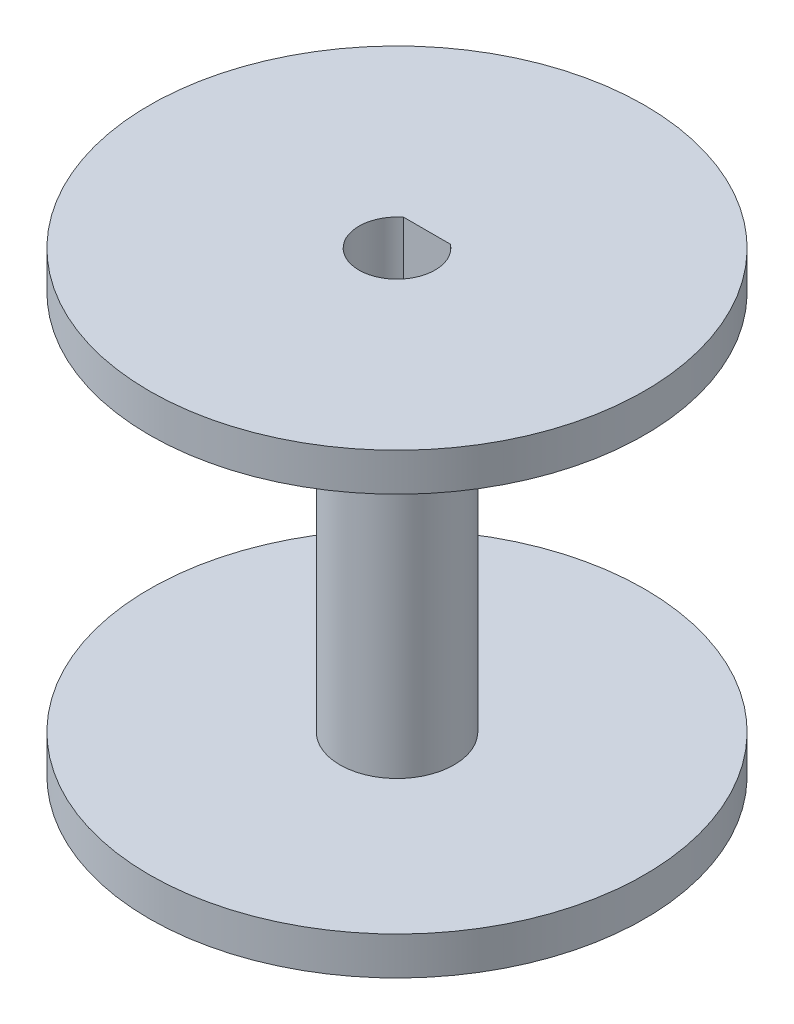
SolidWorks part; units mm, degrees
ref_plane "Front Plane" through (0, 0, 0) normal (0, 0, 1) x (1, 0, 0)
ref_plane "Top Plane" through (0, 0, 0) normal (0, 1, 0) x (1, 0, 0)
ref_plane "Right Plane" through (0, 0, 0) normal (1, 0, 0) x (0, 0, -1)
sketch "Sketch1" plane through (0, 0, 0) normal (0, 1, 0) x (1, 0, 0)
  circle A0 centre (0, 0) radius 33.02
extrude "Boss-Extrude1" add sketch "Sketch1" along normal blind 2.54
sketch "Sketch2" plane through (0, 2.54, 0) normal (0, 1, 0) x (1, 0, 0)
  circle A0 centre (0, 0) radius 2.54
  circle A1 centre (0, 0) radius 3.81
extrude "Boss-Extrude2" add sketch "Sketch2" along normal blind 25.4
sketch "Sketch3" plane through (0, 2.54, 0) normal (0, 1, 0) x (1, 0, 0)
  circle A0 centre (0, 0) radius 2.54
extrude "Cut-Extrude1" cut sketch "Sketch3" against normal blind 25.4
sketch "Sketch4" plane through (0, 27.94, 0) normal (0, 1, 0) x (1, 0, 0)
  circle A0 centre (0, 0) radius 33.02
extrude "Boss-Extrude3" add sketch "Sketch4" along normal blind 2.54
sketch "Sketch5" plane through (0, 27.94, 0) normal (0, -1, 0) x (1, 0, 0)
  circle A0 centre (0, 0) radius 2.54
extrude "Cut-Extrude2" cut sketch "Sketch5" against normal blind 2.54
sketch "Sketch6" plane through (0, 30.48, 0) normal (0, 1, 0) x (1, 0, 0)
  line L0 (0, -2.54) -> (0, 2.0066)
  line L1 (-1.5573, 2.0066) -> (1.5573, 2.0066)
  circle A0 centre (0, 0) radius 2.54 construction
  arc A1 (-1.5573, 2.0066) -> (1.5573, 2.0066) centre (0, 0) cw
  point P9 (0, 2.0066)
  circle M2 centre (0, 0) radius 2.54
extrude "Boss-Extrude4" add sketch "Sketch6" against normal up to surface (30.48 mm away) contours L1 M2 up to face at (0, 0, 2.54)
sketch "Sketch7" plane through (0, 30.48, 0) normal (0, 1, 0) x (1, 0, 0)
  circle A0 centre (0, 0) radius 2.54
  circle A1 centre (0, 0) radius 16.51
  circle A2 centre (0, 0) radius 33.02
  circle M4 centre (0, 0) radius 33.02
extrude "Cut-Extrude3" cut sketch "Sketch7" against normal blind 132.842 contours A1 M4
